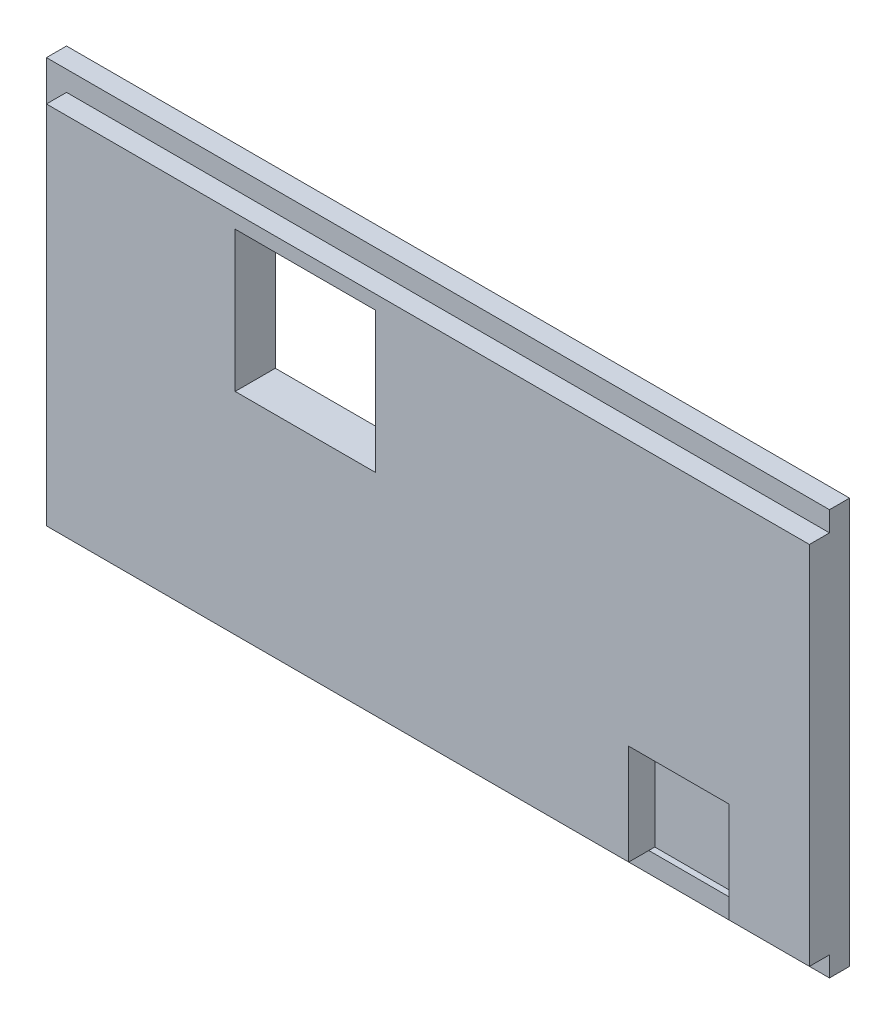
SolidWorks part; units mm, degrees
ref_plane "Front Plane" through (0, 0, 0) normal (0, 0, 1) x (1, 0, 0)
ref_plane "Top Plane" through (0, 0, 0) normal (0, 1, 0) x (1, 0, 0)
ref_plane "Right Plane" through (0, 0, 0) normal (1, 0, 0) x (0, 0, -1)
sketch "Sketch1" plane through (0, 0, 0) normal (0, 0, 1) x (1, 0, 0)
  line L1 (-19.5, 10.1) -> (19.5, 10.1)
  line L2 (-19.5, 10.1) -> (-19.5, -10.1)
  line L3 (-19.5, -10.1) -> (19.5, -10.1)
  line L4 (19.5, 10.1) -> (19.5, -10.1)
  line L5 (-19.5, 10.1) -> (19.5, -10.1) construction
  line L6 (-19.5, -10.1) -> (19.5, 10.1) construction
  point P0 (0, 0)
  dimension "D1" = 39
  dimension "D2" = 20.2
extrude "Boss-Extrude1" add sketch "Sketch1" along normal blind 1
sketch "Sketch2" plane through (0, 0, 1) normal (0, 0, 1) x (1, 0, 0)
  line L0 (19.5, -10.1) -> (19.5, 10.1) construction
  line L1 (-18.5, 9.1) -> (19.5, 9.1)
  line L2 (-18.5, 9.1) -> (-18.5, -9.1)
  line L3 (-18.5, -9.1) -> (19.5, -9.1)
  line L4 (19.5, 9.1) -> (19.5, -9.1)
  line L5 (-19.5, -10.1) -> (19.5, -10.1) construction
  line L6 (19.5, 10.1) -> (-19.5, 10.1) construction
  line L7 (-19.5, 10.1) -> (-19.5, -10.1) construction
  dimension "D1" = 1
  dimension "D2" = 0
  dimension "D3" = 1
  dimension "D4" = 1
extrude "Boss-Extrude2" add sketch "Sketch2" along normal blind 1
sketch "Sketch3" plane through (0, 0, 2) normal (0, 0, 1) x (1, 0, 0)
  line L0 (19.5, -9.1) -> (19.5, 9.1) construction
  line L1 (-9.1, 1.4) -> (-2.1, 1.4)
  line L2 (-9.1, 1.4) -> (-9.1, 8.4)
  line L3 (-9.1, 8.4) -> (-2.1, 8.4)
  line L4 (-2.1, 1.4) -> (-2.1, 8.4)
  line L6 (19.5, 9.1) -> (-18.5, 9.1) construction
  dimension "D1" = 7
  dimension "D2" = 7
  dimension "D3" = 21.6
  dimension "D4" = 0.7
extrude "Cut-Extrude1" cut sketch "Sketch3" against normal blind 21
sketch "Sketch4" plane through (0, 0, 2) normal (0, 0, 1) x (1, 0, 0)
  line L0 (-18.5, -9.1) -> (19.5, -9.1) construction
  line L1 (10.5, -9.1) -> (15.5, -9.1)
  line L2 (10.5, -9.1) -> (10.5, -4.1)
  line L3 (10.5, -4.1) -> (15.5, -4.1)
  line L4 (15.5, -9.1) -> (15.5, -4.1)
  line L6 (19.5, -9.1) -> (19.5, 9.1) construction
  dimension "D1" = 5
  dimension "D2" = 5
  dimension "D3" = 4
extrude "Cut-Extrude2" cut sketch "Sketch4" against normal blind 1.3
